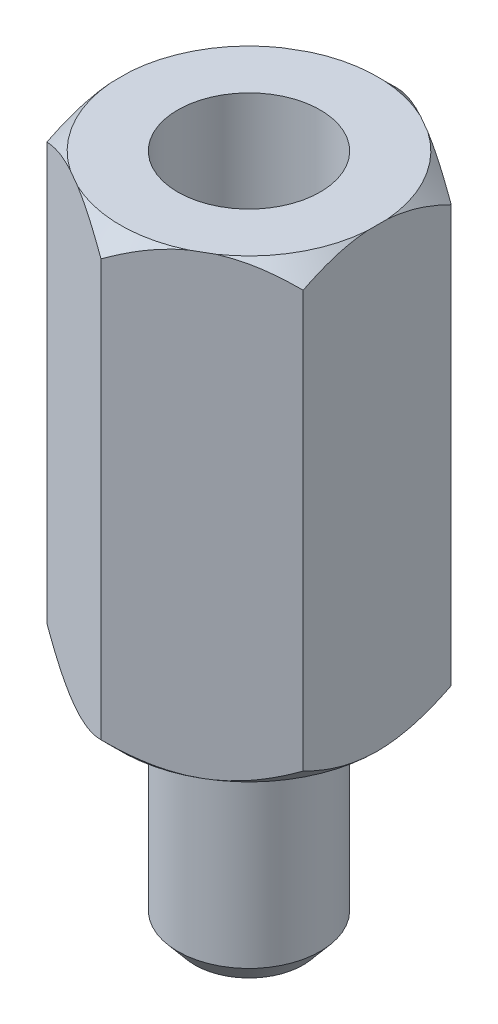
SolidWorks part; units mm, degrees
ref_plane "Front Plane" through (0, 0, 0) normal (0, 0, 1) x (1, 0, 0)
ref_plane "Top Plane" through (0, 0, 0) normal (0, 1, 0) x (1, 0, 0)
ref_plane "Right Plane" through (0, 0, 0) normal (1, 0, 0) x (0, 0, -1)
sketch "Sketch1" plane through (0, 0, 0) normal (0, 1, 0) x (1, 0, 0)
  circle A0 centre (0, 0) radius 1.25
  dimension "D1" = 2.5
extrude "Boss-Extrude1" add sketch "Sketch1" along normal blind 3.9
sketch "Sketch3" plane through (0, 3.9, 0) normal (0, 1, 0) x (1, 0, 0)
  line L1 (-2.25, 1.299) -> (-2.25, -1.299)
  line L2 (-2.25, -1.299) -> (0, -2.5981)
  line L3 (0, -2.5981) -> (2.25, -1.299)
  line L4 (2.25, -1.299) -> (2.25, 1.299)
  line L5 (2.25, 1.299) -> (0, 2.5981)
  line L6 (0, 2.5981) -> (-2.25, 1.299)
  circle A0 centre (0, 0) radius 2.25 construction
  dimension "D1" = 4.5
extrude "Boss-Extrude2" add sketch "Sketch3" along normal blind 8
sketch "Sketch4" plane through (0, 11.9, 0) normal (0, 1, 0) x (1, 0, 0)
  circle A0 centre (0, 0) radius 1.25
  dimension "D1" = 2.5
extrude "Cut-Extrude1" cut sketch "Sketch4" against normal blind 4.8
sketch "Sketch5" plane through (0, 11.9, 0) normal (0, 1, 0) x (1, 0, 0)
  circle A0 centre (0, 0) radius 2.257
extrude "Cut-Extrude2" cut sketch "Sketch5" against normal through all draft 45 flip side to cut
sketch "Sketch6" plane through (0, 3.9, 0) normal (0, -1, 0) x (1, 0, 0)
  circle A0 centre (0, 0) radius 2.25
extrude "Cut-Extrude3" cut sketch "Sketch6" against normal through all draft 45 flip side to cut
chamfer "Chamfer1" distance 0.3 angle 50 1 edges at (0, 0, 1.25)
